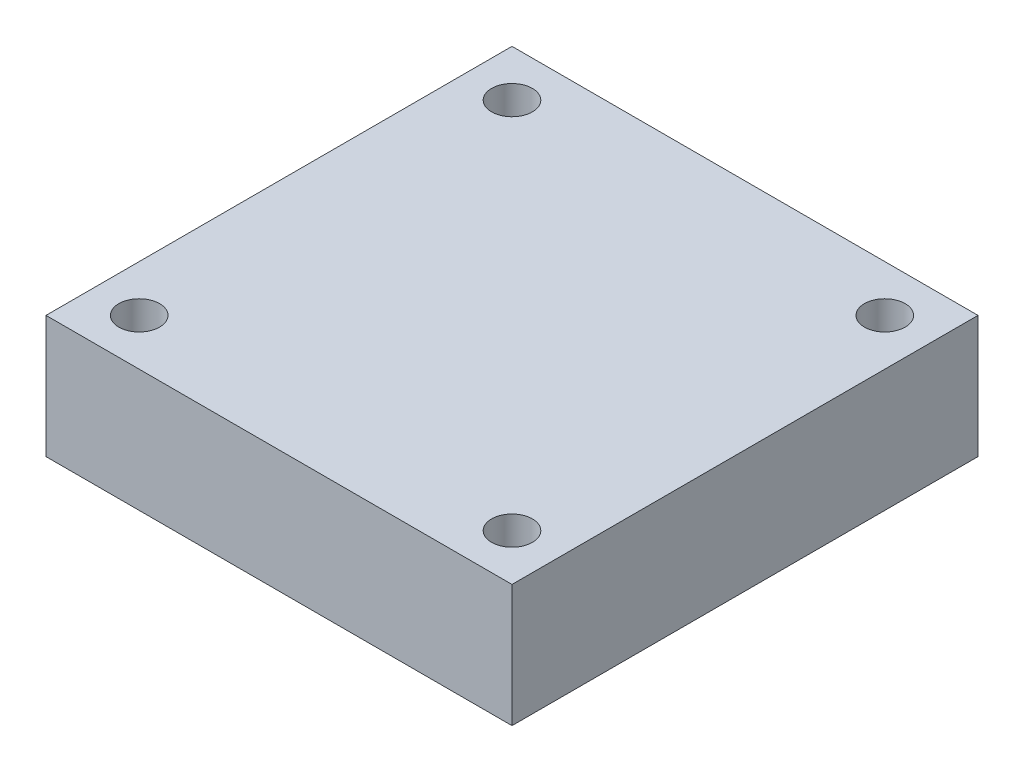
SolidWorks part; units mm, degrees
ref_plane "Front Plane" through (0, 0, 0) normal (0, 0, 1) x (1, 0, 0)
ref_plane "Top Plane" through (0, 0, 0) normal (0, 1, 0) x (1, 0, 0)
ref_plane "Right Plane" through (0, 0, 0) normal (1, 0, 0) x (0, 0, -1)
sketch "Sketch1" plane through (0, 0, 0) normal (0, 1, 0) x (1, 0, 0)
  line L1 (20, -20) -> (-20, -20)
  line L2 (20, -20) -> (20, 20)
  line L3 (20, 20) -> (-20, 20)
  line L4 (-20, -20) -> (-20, 20)
  line L5 (20, -20) -> (-20, 20) construction
  line L6 (20, 20) -> (-20, -20) construction
  point P0 (0, 0)
  dimension "D1" = 40
  dimension "D2" = 40
extrude "Boss-Extrude1" add sketch "Sketch1" along normal blind 10.5
sketch "Sketch2" plane through (0, 10.5, 0) normal (0, 1, 0) x (1, 0, 0)
  line L1 (16, -16) -> (-16, -16) construction
  line L2 (16, -16) -> (16, 16) construction
  line L3 (16, 16) -> (-16, 16) construction
  line L4 (-16, -16) -> (-16, 16) construction
  line L5 (16, -16) -> (-16, 16) construction
  line L6 (16, 16) -> (-16, -16) construction
  circle A0 centre (-16, 16) radius 1.75
  circle A1 centre (16, 16) radius 1.75
  circle A2 centre (16, -16) radius 1.75
  circle A3 centre (-16, -16) radius 1.75
  point P0 (0, 0)
  dimension "D3" = 3.5
  dimension "D4" = 3.5
  dimension "D5" = 3.5
  dimension "D6" = 3.5
  dimension "D1" = 32
  dimension "D2" = 32
extrude "Cut-Extrude1" cut sketch "Sketch2" against normal blind 10.5
